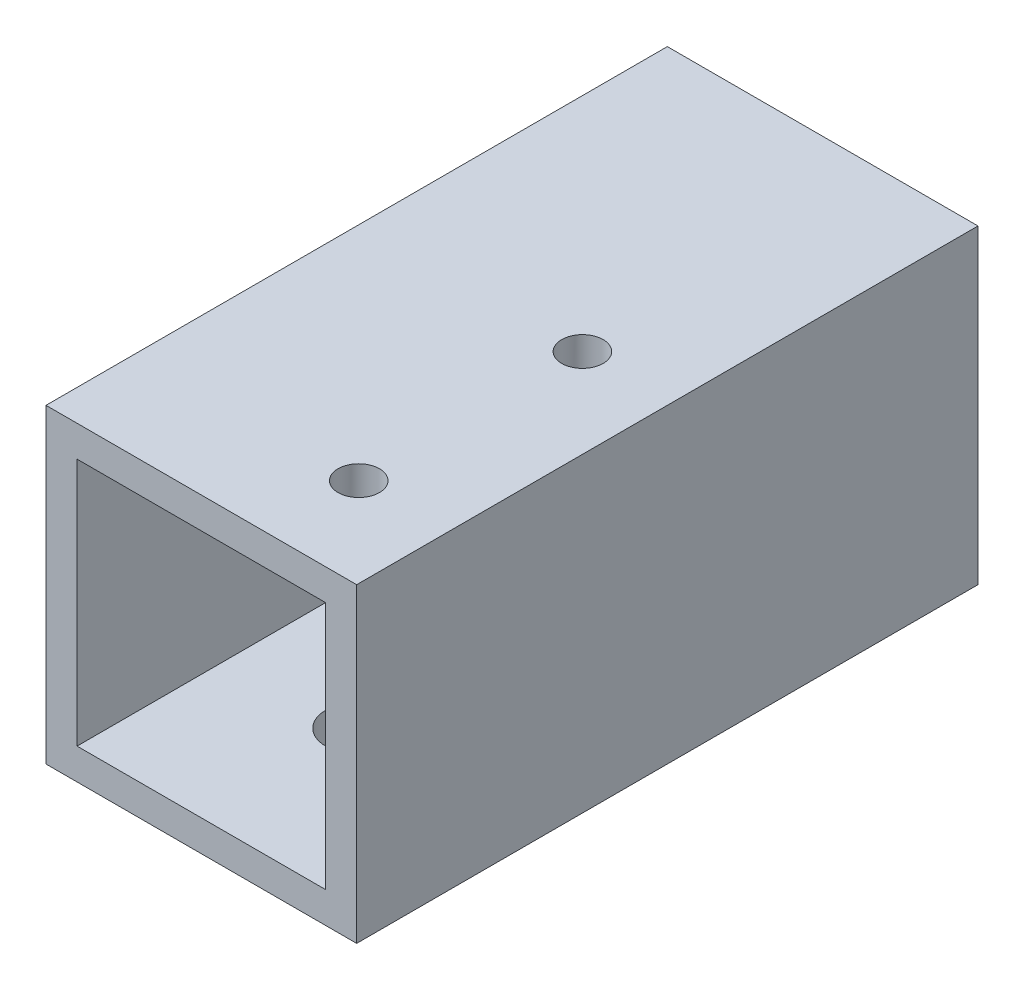
SolidWorks part; units mm, degrees
material "1060 合金"
ref_plane "正面" through (0, 0, 0) normal (0, 0, 1) x (1, 0, 0)
ref_plane "平面" through (0, 0, 0) normal (0, 1, 0) x (1, 0, 0)
ref_plane "右側面" through (0, 0, 0) normal (1, 0, 0) x (0, 0, -1)
sketch "ｽｹｯﾁ1" plane through (0, 0, 0) normal (0, 0, 1) x (1, 0, 0)
  line L1 (-7.0101, 7.7326) -> (7.9899, 7.7326)
  line L2 (-7.0101, 7.7326) -> (-7.0101, -7.2674)
  line L3 (-7.0101, -7.2674) -> (7.9899, -7.2674)
  line L4 (7.9899, 7.7326) -> (7.9899, -7.2674)
  line L9 (-5.5101, 6.2326) -> (6.4899, 6.2326)
  line L10 (-5.5101, 6.2326) -> (-5.5101, -5.7674)
  line L11 (-5.5101, -5.7674) -> (6.4899, -5.7674)
  line L12 (6.4899, 6.2326) -> (6.4899, -5.7674)
  dimension "D1" = 15
  dimension "D2" = 15
  dimension "D3" = 1.5
  dimension "D4" = 1.5
  dimension "D5" = 12
  dimension "D6" = 12
extrude "ﾎﾞｽ - 押し出し2" add sketch "ｽｹｯﾁ1" along normal blind 30
sketch "ｽｹｯﾁ2" plane through (0, 7.7326, 0) normal (0, 1, 0) x (1, 0, 0)
  line L0 (7.9899, -30) -> (7.9899, 0) construction
  line L1 (7.9899, -30) -> (-7.0101, -30) construction
  circle A0 centre (3.6899, -25.6) radius 1
  circle A1 centre (3.6899, -14.8) radius 1
  dimension "D1" = 4.3
  dimension "D2" = 4.4
  dimension "D3" = 10.8
  dimension "D4" = 4.3
extrude "ｶｯﾄ - 押し出し1" cut sketch "ｽｹｯﾁ2" against normal blind 10
sketch "ｽｹｯﾁ3" plane through (-7.0101, 0, 0) normal (-1, 0, 0) x (0, 0, 1)
  line L0 (0, 7.7326) -> (0, -7.2674) construction
  circle A0 centre (7.5, 0.2326) radius 1.5
  dimension "D1" = 7.5
extrude "ｶｯﾄ - 押し出し2" cut sketch "ｽｹｯﾁ3" against normal blind 10
sketch "ｽｹｯﾁ5" plane through (0, -7.2674, 0) normal (0, -1, 0) x (1, 0, 0)
  line L0 (-7.0101, 30) -> (7.9899, 30) construction
  circle A0 centre (0.4899, 22.5) radius 1.5
  dimension "D1" = 7.5
extrude "ｶｯﾄ - 押し出し4" cut sketch "ｽｹｯﾁ5" against normal blind 10
